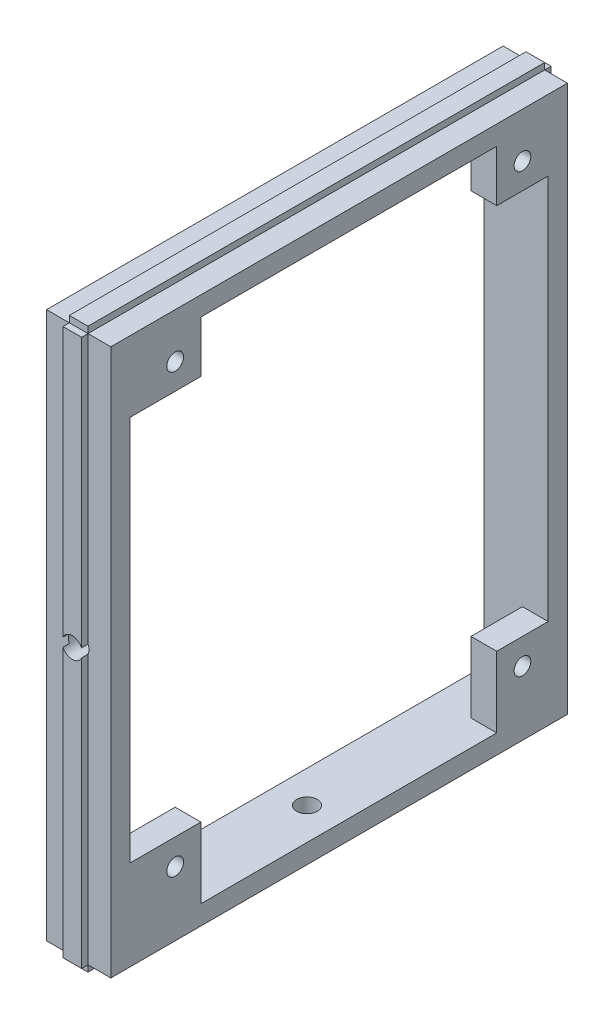
SolidWorks part; units mm, degrees
ref_plane "Front Plane" through (0, 0, 0) normal (0, 0, 1) x (1, 0, 0)
ref_plane "Top Plane" through (0, 0, 0) normal (0, 1, 0) x (1, 0, 0)
ref_plane "Right Plane" through (0, 0, 0) normal (1, 0, 0) x (0, 0, -1)
sketch "Sketch1" plane through (0, 0, 0) normal (0, 0, 1) x (1, 0, 0)
  line L0 (0, 85) -> (3.55, 85)
  line L1 (3.55, 85) -> (3.55, 86)
  line L2 (3.55, 86) -> (6.45, 86)
  line L3 (6.45, 86) -> (6.45, 85)
  line L4 (6.45, 85) -> (10, 85)
  line L5 (10, 85) -> (10, 0)
  line L10 (0, 0) -> (3.55, 0)
  line L11 (0, 0) -> (0, 85)
  line L12 (3.55, 0) -> (3.55, -1)
  line L13 (3.55, -1) -> (6.45, -1)
  line L14 (6.45, -1) -> (6.45, 0)
  line L15 (6.45, 0) -> (10, 0)
  point P5 (0, 0)
  point P9 (25.146, 64.9437)
  point P10 (11.5939, 0)
  point P21 (3.5988, 0)
  point P23 (3.55, 76)
  point P24 (11.7747, 3.55)
  point P25 (12.5179, 72.8873)
  dimension "D1" = 1
  dimension "D2" = 2.9
  dimension "D4" = 3.55
  dimension "D5" = 85
extrude "Main" add sketch "Sketch1" along normal blind 71
sketch "Sketch2" plane through (0, 0, 71) normal (0, 0, 1) x (1, 0, 0)
  line L1 (3.55, 85) -> (6.45, 85)
  line L2 (3.55, 85) -> (3.55, 0)
  line L3 (3.55, 0) -> (6.45, 0)
  line L4 (6.45, 85) -> (6.45, 0)
extrude "MakerBeamRail1" add sketch "Sketch2" along normal blind 1
sketch "Sketch3" plane through (0, 0, 0) normal (0, 0, -1) x (-1, 0, 0)
  line L1 (-6.45, 85) -> (-3.55, 85)
  line L2 (-6.45, 85) -> (-6.45, 0)
  line L3 (-6.45, 0) -> (-3.55, 0)
  line L4 (-3.55, 85) -> (-3.55, 0)
extrude "MakerBeamRail2" add sketch "Sketch3" along normal blind 1
sketch "Sketch4" plane through (0, 0, 0) normal (-1, 0, 0) x (0, 0, 1)
  line L0 (71, 85) -> (0, 85) construction
  line L1 (3, 82) -> (68, 82)
  line L2 (3, 82) -> (3, 3)
  line L3 (3, 3) -> (68, 3)
  line L4 (68, 82) -> (68, 3)
  line L5 (0, 85) -> (0, 0) construction
  dimension "D1" = 79
  dimension "D2" = 65
  dimension "D3" = 3
  dimension "D4" = 3
extrude "BoardCut" cut sketch "Sketch4" against normal blind 6
sketch "Sketch5" plane through (6, 0, 0) normal (-1, 0, 0) x (0, 0, 1)
  line L0 (3, 82) -> (3, 3) construction
  line L2 (68, 82) -> (3, 82) construction
  circle A0 centre (7, 78) radius 1.3
  circle A1 centre (61, 78) radius 1.3
  circle A2 centre (61, 10) radius 1.3
  circle A3 centre (7, 10) radius 1.3
  point P12 (7.913, 82)
  point P13 (0, 0)
  point P14 (0, 0)
  point P15 (0, 0)
  point P16 (0, 0)
  dimension "D1" = 2.6
  dimension "D2" = 54
  dimension "D3" = 4
  dimension "D4" = 4
  dimension "D5" = 68
extrude "BoardHoles" cut sketch "Sketch5" against normal through all
sketch "Sketch6" plane through (0, 0, 72) normal (0, 0, 1) x (1, 0, 0)
  line L1 (10, 0) -> (10, 85) construction
  circle A0 centre (5, 42.5) radius 1.6
  point P2 (10, 42.5)
  point P3 (0, 0)
  point P6 (0, 0)
  dimension "D1" = 3.2
  dimension "D2" = 5
extrude "FixHole1" cut sketch "Sketch6" against normal up to surface (4 mm away) up to face at (3, 42.5, 68)
sketch "Sketch7" plane through (6, 0, 0) normal (-1, 0, 0) x (0, 0, 1)
  line L0 (68, 3) -> (68, 41.251) construction
  line L1 (3, 74) -> (11, 74)
  line L2 (3, 74) -> (3, 14)
  line L3 (3, 14) -> (11, 14)
  line L4 (68, 74) -> (68, 14)
  line L5 (3, 82) -> (3, 3) construction
  line L7 (11, 74) -> (11, 82)
  line L8 (68, 82) -> (3, 82) construction
  line L9 (11, 82) -> (57, 82)
  line L10 (68, 82) -> (3, 82) construction
  line L11 (57, 82) -> (57, 74)
  line L12 (57, 74) -> (68, 74)
  line L13 (11, 14) -> (11, 3)
  line L14 (3, 3) -> (68, 3) construction
  line L15 (11, 3) -> (57, 3)
  line L16 (57, 3) -> (57, 14)
  line L17 (57, 14) -> (68, 14)
  line L18 (68, 43.749) -> (68, 82) construction
  dimension "D1" = 8
  dimension "D2" = 8
  dimension "D3" = 11
  dimension "D4" = 11
extrude "MainHole" cut sketch "Sketch7" against normal through all
sketch "Sketch8" plane through (0, -1, 0) normal (0, -1, 0) x (-1, 0, 0)
  line L1 (-10, -71) -> (-10, 0) construction
  circle A0 centre (-5, -35.5) radius 1.6
  point P2 (-10, -35.5)
  point P3 (0, 0)
  point P4 (0, 0)
  point P5 (0, 0)
  dimension "D1" = 3.2
  dimension "D2" = 5
extrude "FixHole2" cut sketch "Sketch8" against normal up to next
